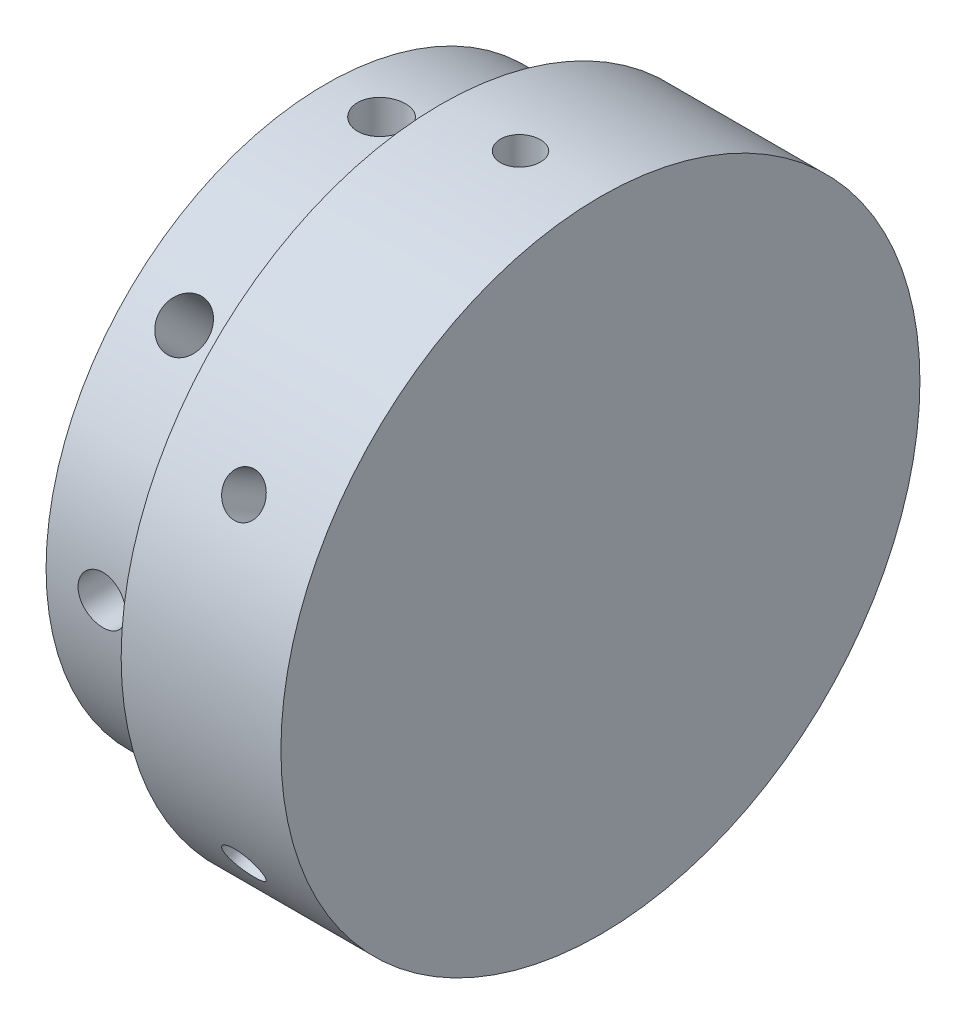
SolidWorks part; units mm, degrees
ref_plane "Front Plane" through (0, 0, 0) normal (0, 0, 1) x (1, 0, 0)
ref_plane "Top Plane" through (0, 0, 0) normal (0, 1, 0) x (1, 0, 0)
ref_plane "Right Plane" through (0, 0, 0) normal (1, 0, 0) x (0, 0, -1)
sketch "Sketch1" plane through (0, 0, 0) normal (1, 0, 0) x (0, 0, -1)
  circle A0 centre (0, 0) radius 30
  circle A1 centre (0, 0) radius 40
  dimension "D1" = 60
  dimension "D2" = 80
extrude "Boss-Extrude2" add sketch "Sketch1" along normal mid plane 20 contours A1
sketch "Sketch3" plane through (-10, 0, 0) normal (-1, 0, 0) x (0, 0, 1)
  circle A0 centre (0, 0) radius 35
  dimension "D1" = 70
ref_plane "Top Bolts" through (0, 40, 0) normal (0, 1, 0) x (1, 0, 0)
sketch "Sketch4" plane through (0, 40, 0) normal (0, 1, 0) x (1, 0, 0)
  line L0 (0, 0) -> (-10, 0) construction
  line L1 (-10, 40) -> (-10, -40) construction
  circle A0 centre (0, 0) radius 2.5
  point P5 (0, 0)
  dimension "D1" = 5
  dimension "D2" = 10
extrude "Cut-Extrude3" cut sketch "Sketch4" against normal blind 15.4
pattern_circular "CirPattern1" count 6 over 360 about axis through (0, 0, 0) along (1, 0, 0) of "Cut-Extrude3"
extrude "Boss-Extrude4" add sketch "Sketch3" along normal blind 14.4 contours A0
ref_plane "Plane1" through (0, 35, 0) normal (0, 1, 0) x (1, 0, 0)
sketch "Sketch8" plane through (0, 35, 0) normal (0, 1, 0) x (1, 0, 0)
  line L0 (-24.4, 0) -> (-17.4, 0) construction
  line L1 (-24.4, 35) -> (-24.4, -35) construction
  circle A0 centre (-17.4, 0) radius 3
  dimension "D1" = 7
extrude "Cut-Extrude4" cut sketch "Sketch8" against normal blind 10
pattern_circular "CirPattern2" count 8 over 360 about axis through (0, 0, 0) along (1, 0, 0) of "Cut-Extrude4"
